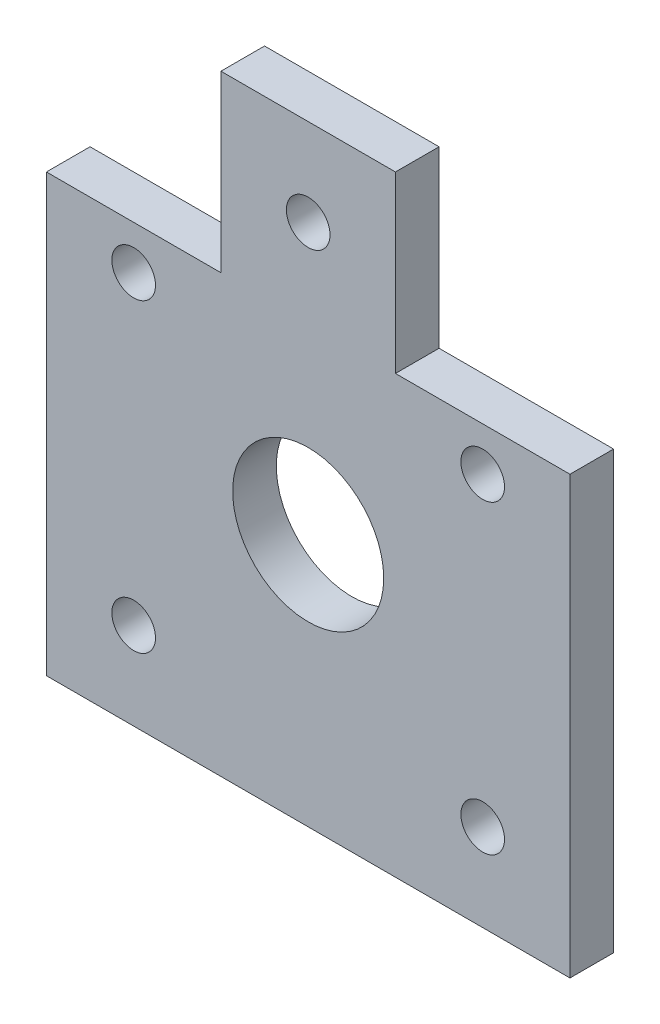
SolidWorks part; units mm, degrees
ref_plane "Front Plane" through (0, 0, 0) normal (0, 0, 1) x (1, 0, 0)
ref_plane "Top Plane" through (0, 0, 0) normal (0, 1, 0) x (1, 0, 0)
ref_plane "Right Plane" through (0, 0, 0) normal (1, 0, 0) x (0, 0, -1)
sketch "Sketch1" plane through (0, 0, 0) normal (0, 0, 1) x (1, 0, 0)
  line L1 (0, 0) -> (76.2, 0)
  line L2 (0, 0) -> (0, 88.9)
  line L3 (0, 88.9) -> (76.2, 88.9)
  line L4 (76.2, 0) -> (76.2, 88.9)
  dimension "D1" = 88.9
  dimension "D2" = 76.2
extrude "Boss-Extrude1" add sketch "Sketch1" along normal mid plane 6.35
sketch "Sketch2" plane through (0, 0, 3.175) normal (0, 0, 1) x (1, 0, 0)
  line L0 (38.1, 88.9) -> (38.1, 0) construction
  line L1 (63.5, 12.7) -> (12.7, 12.7) construction
  line L2 (63.5, 12.7) -> (63.5, 76.2) construction
  line L3 (63.5, 76.2) -> (12.7, 76.2) construction
  line L4 (12.7, 12.7) -> (12.7, 76.2) construction
  line L5 (63.5, 12.7) -> (12.7, 76.2) construction
  line L6 (63.5, 76.2) -> (12.7, 12.7) construction
  line L7 (76.2, 88.9) -> (0, 88.9) construction
  line L8 (0, 0) -> (76.2, 0) construction
  line L9 (12.7, 57.15) -> (63.5, 57.15) construction
  line L11 (0, 88.9) -> (0, 0) construction
  circle A0 centre (12.7, 76.2) radius 3.175
  circle A1 centre (63.5, 76.2) radius 3.175
  circle A2 centre (63.5, 12.7) radius 3.175
  circle A3 centre (12.7, 12.7) radius 3.175
  circle A4 centre (38.1, 36.83) radius 10.9918
  circle A5 centre (12.7, 57.15) radius 3.175
  circle A6 centre (63.5, 57.15) radius 3.175
  point P0 (38.1, 44.45)
  point P22 (38.1, 57.15)
  point P28 (38.1, 44.45)
  point P30 (38.1, 44.45)
  dimension "D2" = 6.35
  dimension "D3" = 21.9837
  dimension "D4" = 6.35
  dimension "D1" = 12.7
  dimension "D5" = 50.8
  dimension "D6" = 12.7
  dimension "D7" = 7.62
  dimension "D8" = 12.7
extrude "Cut-Extrude1" cut sketch "Sketch2" against normal through all
sketch "Sketch3" plane through (0, 0, 3.175) normal (0, 0, 1) x (1, 0, 0)
  line L0 (28.5299, 69.5684) -> (62.9645, 69.5684) construction
  text T0 "<b>Front</b>"
sketch "Sketch4" plane through (0, 0, 3.175) normal (0, 0, 1) x (1, 0, 0)
  line L1 (38.1, 36.83) -> (8.8361, 36.83) construction
  line L2 (38.1, 36.83) -> (87.0547, 19.0119) construction
  line L3 (38.1, 36.83) -> (-10.8547, 54.6481) construction
  dimension "D1" = 160
sketch "Sketch5" plane through (0, 0, 3.175) normal (0, 0, 1) x (1, 0, 0)
  line L1 (76.2, 88.9) -> (50.8, 88.9)
  line L2 (76.2, 88.9) -> (76.2, 63.5)
  line L3 (76.2, 63.5) -> (50.8, 63.5)
  line L4 (50.8, 88.9) -> (50.8, 63.5)
  line L5 (0, 88.9) -> (25.4, 88.9)
  line L6 (0, 88.9) -> (0, 63.5)
  line L7 (0, 63.5) -> (25.4, 63.5)
  line L8 (25.4, 88.9) -> (25.4, 63.5)
  circle A0 centre (38.1, 76.2) radius 3.175
  circle A1 centre (12.7, 76.2) radius 3.175 construction
  point P14 (25.4, 76.2)
  dimension "D1" = 25.4
extrude "Cut-Extrude2" cut sketch "Sketch5" against normal up to next
